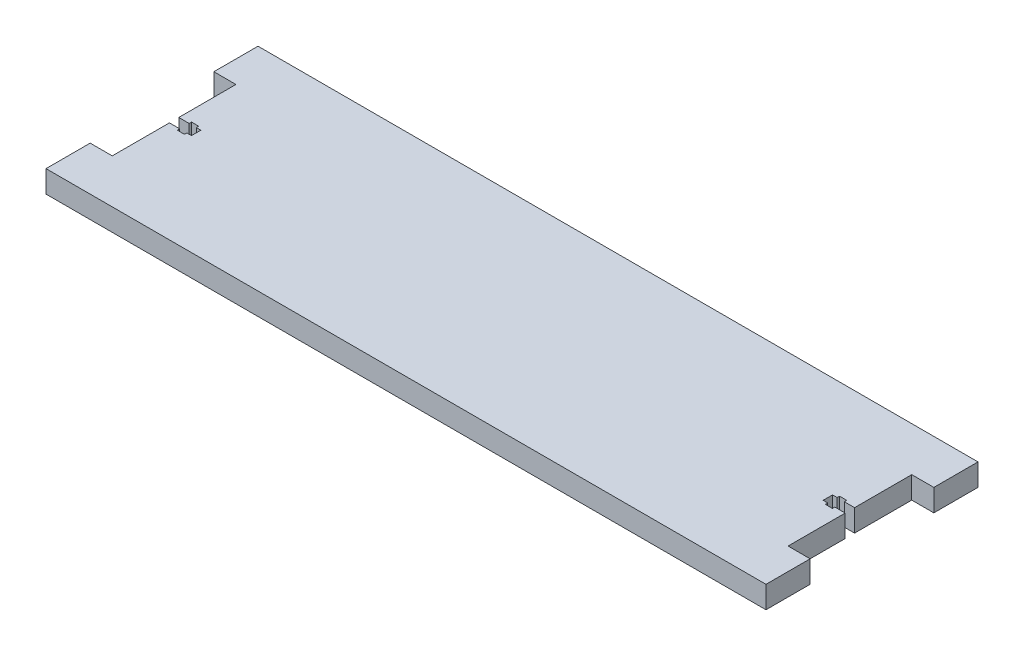
SolidWorks part; units mm, degrees
material "Pine"
ref_plane "Front Plane" through (0, 0, 0) normal (0, 0, 1) x (1, 0, 0)
ref_plane "Top Plane" through (0, 0, 0) normal (0, 1, 0) x (1, 0, 0)
ref_plane "Right Plane" through (0, 0, 0) normal (1, 0, 0) x (0, 0, -1)
sketch "Sketch1" plane through (0, 0, 0) normal (0, 1, 0) x (1, 0, 0)
  line L1 (0, 0) -> (388.62, 0)
  line L2 (0, 0) -> (0, 121.92)
  line L3 (0, 121.92) -> (388.62, 121.92)
  line L4 (388.62, 0) -> (388.62, 121.92)
  dimension "D1" = 121.92
  dimension "D2" = 388.62
extrude "Boss-Extrude1" add sketch "Sketch1" along normal blind 12.7
sketch "Sketch3" plane through (0, 12.7, 0) normal (0, 1, 0) x (1, 0, 0)
  line L0 (0, 60.96) -> (50000, 60.96) construction
  line L1 (0, 121.92) -> (-12.7, 121.92)
  line L2 (0, 121.92) -> (0, 96.52)
  line L3 (0, 96.52) -> (-12.7, 96.52)
  line L4 (-12.7, 121.92) -> (-12.7, 96.52)
  line L5 (0, 121.92) -> (0, 0) construction
  line L6 (194.31, 116.84) -> (194.31, 50116.84) construction
  line L7 (388.62, 121.92) -> (0, 121.92) construction
  line L8 (-12.7, 0) -> (-12.7, 25.4)
  line L9 (0, 25.4) -> (-12.7, 25.4)
  line L10 (0, 0) -> (0, 25.4)
  line L11 (0, 0) -> (-12.7, 0)
  line L12 (388.62, 0) -> (401.32, 0)
  line L13 (388.62, 0) -> (388.62, 25.4)
  line L14 (388.62, 25.4) -> (401.32, 25.4)
  line L15 (401.32, 0) -> (401.32, 25.4)
  line L16 (401.32, 121.92) -> (401.32, 96.52)
  line L17 (388.62, 96.52) -> (401.32, 96.52)
  line L18 (388.62, 121.92) -> (388.62, 96.52)
  line L19 (388.62, 121.92) -> (401.32, 121.92)
  point P9 (0, 60.96)
  point P14 (194.31, 121.92)
  dimension "D1" = 25.4
  dimension "D2" = 12.7
extrude "tabs" add sketch "Sketch3" against normal up to surface (12.7 mm away) up to face at (194.31, 0, -60.96)
sketch "Sketch4" plane through (0, 0, 0) normal (-1, 0, 0) x (0, 0, 1)
  line L0 (-96.52, 6.35) -> (-25.4, 6.35) construction
  line L1 (-96.52, 0) -> (-96.52, 12.7) construction
  line L2 (-25.4, 0) -> (-25.4, 12.7) construction
  line L3 (-96.52, 12.7) -> (-25.4, 12.7) construction
  line L4 (-63.66, 0) -> (-58.26, 0)
  line L5 (-63.66, 0) -> (-63.66, 12.7)
  line L6 (-63.66, 12.7) -> (-58.26, 12.7)
  line L7 (-58.26, 0) -> (-58.26, 12.7)
  line L8 (-63.66, 0) -> (-58.26, 12.7) construction
  line L9 (-63.66, 12.7) -> (-58.26, 0) construction
  circle A0 centre (-60.96, 6.35) radius 2.5 construction
  dimension "D1" = 5
  dimension "D2" = 5.4
extrude "screw slot" cut sketch "Sketch4" against normal blind 12.7
sketch "Sketch5" plane through (0, 12.7, 0) normal (0, 1, 0) x (1, 0, 0)
  line L0 (12.7, 60.96) -> (0, 60.96) construction
  line L1 (12.7, 58.26) -> (12.7, 63.66) construction
  line L3 (10.05, 56.885) -> (5.95, 56.885)
  line L4 (10.05, 56.885) -> (10.05, 65.035)
  line L5 (10.05, 65.035) -> (5.95, 65.035)
  line L6 (5.95, 56.885) -> (5.95, 65.035)
  line L7 (10.05, 56.885) -> (5.95, 65.035) construction
  line L8 (10.05, 65.035) -> (5.95, 56.885) construction
  point P4 (8, 60.96)
  dimension "D1" = 12.7
  dimension "D2" = 4.1
  dimension "D3" = 8.15
  dimension "D4" = 8
extrude "nut slot" cut sketch "Sketch5" against normal up to surface (12.7 mm away) up to face at (147.32, 0, -60.7912)
ref_plane "Plane1" through (194.31, 0, 0) normal (1, 0, 0) x (0, 0, -1)
mirror "Mirror1" about plane through (194.31, 0, 0) normal (1, 0, 0) of "screw slot", "nut slot"
sketch "Sketch6" plane through (0, 12.7, 0) normal (0, 1, 0) x (1, 0, 0)
  line L0 (194.31, 0) -> (194.31, 121.92) construction
  line L1 (-12.7, 0) -> (401.32, 0) construction
  line L2 (401.32, 121.92) -> (-12.7, 121.92) construction
  circle A0 centre (189.23, 5.08) radius 1.5
  circle A1 centre (199.39, 5.08) radius 1.5
  dimension "D1" = 3
  dimension "D2" = 5.08
  dimension "D3" = 5.08
equation "\"t\"= .5in"
